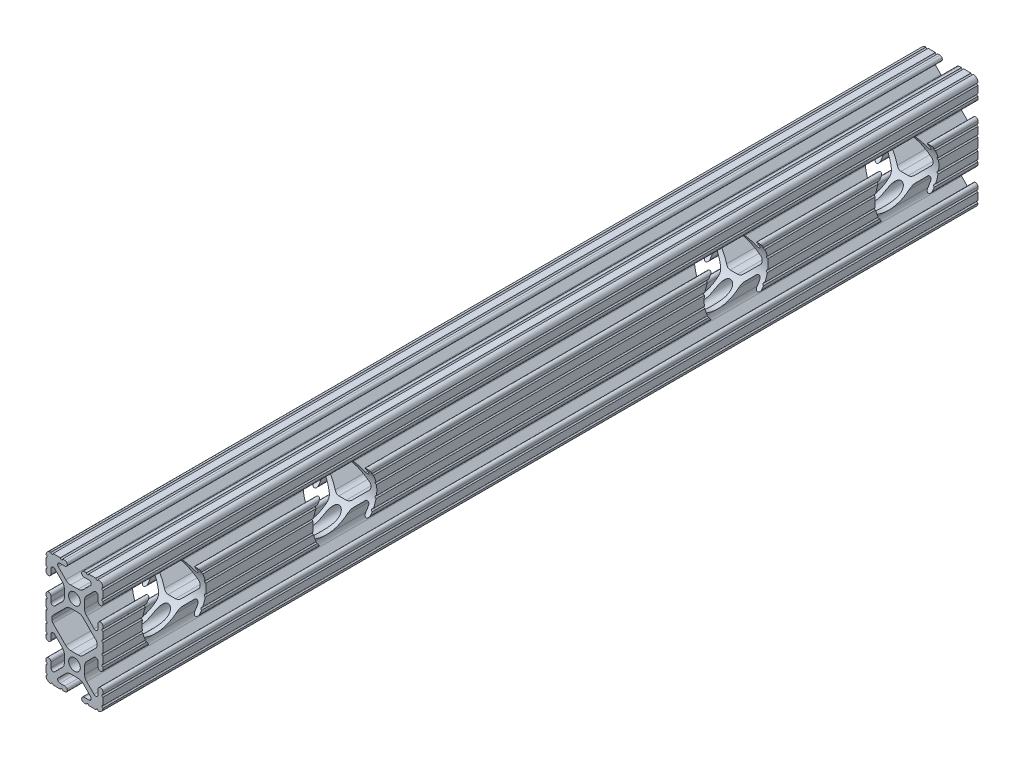
SolidWorks part; units mm, degrees
material "6061-T6 (SS)"
ref_plane "Front Plane" through (0, 0, 0) normal (0, 0, 1) x (1, 0, 0)
ref_plane "Top Plane" through (0, 0, 0) normal (0, 1, 0) x (1, 0, 0)
ref_plane "Right Plane" through (0, 0, 0) normal (1, 0, 0) x (0, 0, -1)
ref_plane "Plane1" through (0, 0, -889) normal (0, 0, -1) x (-1, 0, 0)
sketch "Sketch1" plane through (0, 0, -889) normal (0, 0, -1) x (-1, 0, 0)
  line L0 (10.033, 13.1521) -> (10.033, 12.2479)
  line L1 (9.5718, 11.1343) -> (3.8759, 5.4384)
  line L2 (1.6308, 4.5085) -> (-1.6308, 4.5085)
  line L3 (-3.8759, 5.4384) -> (-9.5718, 11.1343)
  line L4 (-10.033, 12.2479) -> (-10.033, 13.1521)
  line L5 (-9.5718, 14.2657) -> (-3.8759, 19.9616)
  line L6 (-1.6308, 20.8915) -> (1.6308, 20.8915)
  line L7 (3.8759, 19.9616) -> (9.5718, 14.2657)
  line L8 (9.5504, 38.1) -> (6.3246, 38.1)
  line L9 (5.3086, 38.1) -> (4.3023, 38.1)
  line L10 (4.3023, 35.8902) -> (6.4748, 35.8902)
  line L11 (7.1932, 34.1558) -> (3.8759, 30.8384)
  line L12 (1.6308, 29.9085) -> (-1.6308, 29.9085)
  line L13 (-3.8759, 30.8384) -> (-7.1932, 34.1558)
  line L14 (-6.4748, 35.8902) -> (-4.3023, 35.8902)
  line L15 (-4.3023, 38.1) -> (-5.3086, 38.1)
  line L16 (-6.3246, 38.1) -> (-9.5504, 38.1)
  line L17 (-12.7, 34.9504) -> (-12.7, 31.7246)
  line L18 (-12.7, 30.7086) -> (-12.7, 29.7023)
  line L19 (-10.4902, 29.7023) -> (-10.4902, 31.8748)
  line L20 (-8.7558, 32.5932) -> (-5.4384, 29.2759)
  line L21 (-4.5085, 27.0308) -> (-4.5085, 23.7692)
  line L22 (-5.4384, 21.5241) -> (-8.7558, 18.2068)
  line L23 (-10.4902, 18.9252) -> (-10.4902, 21.0977)
  line L24 (-12.7, 21.0977) -> (-12.7, 20.0914)
  line L25 (-12.7, 19.0754) -> (-12.7, 15.8496)
  line L26 (-12.7, 14.8336) -> (-12.7, 10.5664)
  line L27 (-12.7, 9.5504) -> (-12.7, 6.3246)
  line L28 (-12.7, 5.3086) -> (-12.7, 4.3023)
  line L29 (-10.4902, 4.3023) -> (-10.4902, 6.4748)
  line L30 (-8.7558, 7.1932) -> (-5.4384, 3.8759)
  line L31 (-4.5085, 1.6308) -> (-4.5085, -1.6308)
  line L32 (-5.4384, -3.8759) -> (-8.7558, -7.1932)
  line L33 (-10.4902, -6.4748) -> (-10.4902, -4.3023)
  line L34 (-12.7, -4.3023) -> (-12.7, -5.3086)
  line L35 (-12.7, -6.3246) -> (-12.7, -9.5504)
  line L36 (-9.5504, -12.7) -> (-6.3246, -12.7)
  line L37 (-5.3086, -12.7) -> (-4.3023, -12.7)
  line L38 (-4.3023, -10.4902) -> (-6.4748, -10.4902)
  line L39 (-7.1932, -8.7558) -> (-3.8759, -5.4384)
  line L40 (-1.6308, -4.5085) -> (1.6308, -4.5085)
  line L41 (3.8759, -5.4384) -> (7.1932, -8.7558)
  line L42 (6.4748, -10.4902) -> (4.3023, -10.4902)
  line L43 (4.3023, -12.7) -> (5.3086, -12.7)
  line L44 (6.3246, -12.7) -> (9.5504, -12.7)
  line L45 (12.7, -9.5504) -> (12.7, -6.3246)
  line L46 (12.7, -5.3086) -> (12.7, -4.3023)
  line L47 (10.4902, -4.3023) -> (10.4902, -6.4748)
  line L48 (8.7558, -7.1932) -> (5.4384, -3.8759)
  line L49 (4.5085, -1.6308) -> (4.5085, 1.6308)
  line L50 (5.4384, 3.8759) -> (8.7558, 7.1932)
  line L51 (10.4902, 6.4748) -> (10.4902, 4.3023)
  line L52 (12.7, 4.3023) -> (12.7, 5.3086)
  line L53 (12.7, 6.3246) -> (12.7, 9.5504)
  line L54 (12.7, 10.5664) -> (12.7, 14.8336)
  line L55 (12.7, 15.8496) -> (12.7, 19.0754)
  line L56 (12.7, 20.0914) -> (12.7, 21.0977)
  line L57 (10.4902, 21.0977) -> (10.4902, 18.9252)
  line L58 (8.7558, 18.2068) -> (5.4384, 21.5241)
  line L59 (4.5085, 23.7692) -> (4.5085, 27.0308)
  line L60 (5.4384, 29.2759) -> (8.7558, 32.5932)
  line L61 (10.4902, 31.8748) -> (10.4902, 29.7023)
  line L62 (12.7, 29.7023) -> (12.7, 30.7086)
  line L63 (12.7, 31.7246) -> (12.7, 34.9504)
  arc A0 (10.033, 12.2479) -> (9.5718, 11.1343) centre (8.4582, 12.2479) cw
  arc A1 (3.8759, 5.4384) -> (1.6308, 4.5085) centre (1.6308, 7.6835) cw
  arc A2 (-1.6308, 4.5085) -> (-3.8759, 5.4384) centre (-1.6308, 7.6835) cw
  arc A3 (-9.5718, 11.1343) -> (-10.033, 12.2479) centre (-8.4582, 12.2479) cw
  arc A4 (-10.033, 13.1521) -> (-9.5718, 14.2657) centre (-8.4582, 13.1521) cw
  arc A5 (-3.8759, 19.9616) -> (-1.6308, 20.8915) centre (-1.6308, 17.7165) cw
  arc A6 (1.6308, 20.8915) -> (3.8759, 19.9616) centre (1.6308, 17.7165) cw
  arc A7 (9.5718, 14.2657) -> (10.033, 13.1521) centre (8.4582, 13.1521) cw
  circle A8 centre (0, 25.4) radius 2.6035
  arc A9 (12.7, 35.9791) -> (10.5791, 38.1) centre (10.5918, 35.9918) ccw
  arc A10 (10.5791, 38.1) -> (9.5504, 38.1) centre (10.0647, 38.1063) cw
  arc A11 (6.3246, 38.1) -> (5.3086, 38.1) centre (5.8166, 38.1) cw
  arc A12 (4.3023, 38.1) -> (4.3023, 35.8902) centre (4.3023, 36.9951) ccw
  arc A13 (6.4748, 35.8902) -> (7.1932, 34.1558) centre (6.4748, 34.8742) cw
  arc A14 (3.8759, 30.8384) -> (1.6308, 29.9085) centre (1.6308, 33.0835) cw
  arc A15 (-1.6308, 29.9085) -> (-3.8759, 30.8384) centre (-1.6308, 33.0835) cw
  arc A16 (-7.1932, 34.1558) -> (-6.4748, 35.8902) centre (-6.4748, 34.8742) cw
  arc A17 (-4.3023, 35.8902) -> (-4.3023, 38.1) centre (-4.3023, 36.9951) ccw
  arc A18 (-5.3086, 38.1) -> (-6.3246, 38.1) centre (-5.8166, 38.1) cw
  arc A19 (-9.5504, 38.1) -> (-10.5791, 38.1) centre (-10.0647, 38.1063) cw
  arc A20 (-10.5791, 38.1) -> (-12.7, 35.9791) centre (-10.5918, 35.9918) ccw
  arc A21 (-12.7, 35.9791) -> (-12.7, 34.9504) centre (-12.7063, 35.4647) cw
  arc A22 (-12.7, 31.7246) -> (-12.7, 30.7086) centre (-12.7, 31.2166) cw
  arc A23 (-12.7, 29.7023) -> (-10.4902, 29.7023) centre (-11.5951, 29.7023) ccw
  arc A24 (-10.4902, 31.8748) -> (-8.7558, 32.5932) centre (-9.4742, 31.8748) cw
  arc A25 (-5.4384, 29.2759) -> (-4.5085, 27.0308) centre (-7.6835, 27.0308) cw
  arc A26 (-4.5085, 23.7692) -> (-5.4384, 21.5241) centre (-7.6835, 23.7692) cw
  arc A27 (-8.7558, 18.2068) -> (-10.4902, 18.9252) centre (-9.4742, 18.9252) cw
  arc A28 (-10.4902, 21.0977) -> (-12.7, 21.0977) centre (-11.5951, 21.0977) ccw
  arc A29 (-12.7, 20.0914) -> (-12.7, 19.0754) centre (-12.7, 19.5834) cw
  arc A30 (-12.7, 15.8496) -> (-12.7, 14.8336) centre (-12.7, 15.3416) cw
  arc A31 (-12.7, 10.5664) -> (-12.7, 9.5504) centre (-12.7, 10.0584) cw
  arc A32 (-12.7, 6.3246) -> (-12.7, 5.3086) centre (-12.7, 5.8166) cw
  arc A33 (-12.7, 4.3023) -> (-10.4902, 4.3023) centre (-11.5951, 4.3023) ccw
  arc A34 (-10.4902, 6.4748) -> (-8.7558, 7.1932) centre (-9.4742, 6.4748) cw
  arc A35 (-5.4384, 3.8759) -> (-4.5085, 1.6308) centre (-7.6835, 1.6308) cw
  arc A36 (-4.5085, -1.6308) -> (-5.4384, -3.8759) centre (-7.6835, -1.6308) cw
  arc A37 (-8.7558, -7.1932) -> (-10.4902, -6.4748) centre (-9.4742, -6.4748) cw
  arc A38 (-10.4902, -4.3023) -> (-12.7, -4.3023) centre (-11.5951, -4.3023) ccw
  arc A39 (-12.7, -5.3086) -> (-12.7, -6.3246) centre (-12.7, -5.8166) cw
  arc A40 (-12.7, -9.5504) -> (-12.7, -10.5791) centre (-12.7063, -10.0647) cw
  arc A41 (-12.7, -10.5791) -> (-10.5791, -12.7) centre (-10.5918, -10.5918) ccw
  arc A42 (-10.5791, -12.7) -> (-9.5504, -12.7) centre (-10.0647, -12.7063) cw
  arc A43 (-6.3246, -12.7) -> (-5.3086, -12.7) centre (-5.8166, -12.7) cw
  arc A44 (-4.3023, -12.7) -> (-4.3023, -10.4902) centre (-4.3023, -11.5951) ccw
  arc A45 (-6.4748, -10.4902) -> (-7.1932, -8.7558) centre (-6.4748, -9.4742) cw
  arc A46 (-3.8759, -5.4384) -> (-1.6308, -4.5085) centre (-1.6308, -7.6835) cw
  arc A47 (1.6308, -4.5085) -> (3.8759, -5.4384) centre (1.6308, -7.6835) cw
  arc A48 (7.1932, -8.7558) -> (6.4748, -10.4902) centre (6.4748, -9.4742) cw
  arc A49 (4.3023, -10.4902) -> (4.3023, -12.7) centre (4.3023, -11.5951) ccw
  arc A50 (5.3086, -12.7) -> (6.3246, -12.7) centre (5.8166, -12.7) cw
  arc A51 (9.5504, -12.7) -> (10.5791, -12.7) centre (10.0647, -12.7063) cw
  arc A52 (10.5791, -12.7) -> (12.7, -10.5791) centre (10.5918, -10.5918) ccw
  arc A53 (12.7, -10.5791) -> (12.7, -9.5504) centre (12.7063, -10.0647) cw
  arc A54 (12.7, -6.3246) -> (12.7, -5.3086) centre (12.7, -5.8166) cw
  arc A55 (12.7, -4.3023) -> (10.4902, -4.3023) centre (11.5951, -4.3023) ccw
  arc A56 (10.4902, -6.4748) -> (8.7558, -7.1932) centre (9.4742, -6.4748) cw
  arc A57 (5.4384, -3.8759) -> (4.5085, -1.6308) centre (7.6835, -1.6308) cw
  arc A58 (4.5085, 1.6308) -> (5.4384, 3.8759) centre (7.6835, 1.6308) cw
  arc A59 (8.7558, 7.1932) -> (10.4902, 6.4748) centre (9.4742, 6.4748) cw
  arc A60 (10.4902, 4.3023) -> (12.7, 4.3023) centre (11.5951, 4.3023) ccw
  arc A61 (12.7, 5.3086) -> (12.7, 6.3246) centre (12.7, 5.8166) cw
  arc A62 (12.7, 9.5504) -> (12.7, 10.5664) centre (12.7, 10.0584) cw
  arc A63 (12.7, 14.8336) -> (12.7, 15.8496) centre (12.7, 15.3416) cw
  arc A64 (12.7, 19.0754) -> (12.7, 20.0914) centre (12.7, 19.5834) cw
  arc A65 (12.7, 21.0977) -> (10.4902, 21.0977) centre (11.5951, 21.0977) ccw
  arc A66 (10.4902, 18.9252) -> (8.7558, 18.2068) centre (9.4742, 18.9252) cw
  arc A67 (5.4384, 21.5241) -> (4.5085, 23.7692) centre (7.6835, 23.7692) cw
  arc A68 (4.5085, 27.0308) -> (5.4384, 29.2759) centre (7.6835, 27.0308) cw
  arc A69 (8.7558, 32.5932) -> (10.4902, 31.8748) centre (9.4742, 31.8748) cw
  arc A70 (10.4902, 29.7023) -> (12.7, 29.7023) centre (11.5951, 29.7023) ccw
  arc A71 (12.7, 30.7086) -> (12.7, 31.7246) centre (12.7, 31.2166) cw
  arc A72 (12.7, 34.9504) -> (12.7, 35.9791) centre (12.7063, 35.4647) cw
  circle A73 centre (0, 0) radius 2.6035
extrude "Boss-Extrude1" add sketch "Sketch1" against normal blind 390.5504
ref_plane "Plane2" through (0, 0, -693.7248) normal (0, 0, 1) x (1, 0, 0)
ref_plane "Plane3" through (0, 12.7, 0) normal (0, 1, 0) x (1, 0, 0)
sketch "Sketch2" plane through (12.7, 0, 0) normal (1, 0, 0) x (0, 0, -1)
  line L0 (498.4496, 12.7) -> (889, 12.7) construction
  line L1 (498.4496, 14.8336) -> (498.4496, 10.5664) construction
  line L2 (889, 14.8336) -> (889, 10.5664) construction
  circle A0 centre (530.1996, 12.7) radius 14.2875
  circle A1 centre (606.3996, 12.7) radius 14.2875
  dimension "D1" = 28.575
  dimension "D2" = 31.75
  dimension "D3" = 2
extrude "Cut-Extrude1" cut sketch "Sketch2" against normal through all both and the other way through all
mirror "Mirror1" about plane through (0, 0, -693.7248) normal (0, 0, 1) of "Cut-Extrude1"
